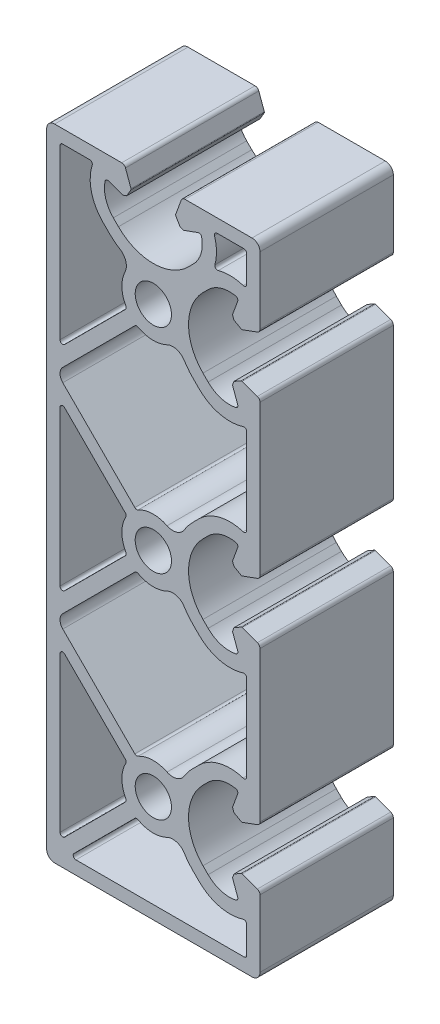
SolidWorks part; units mm, degrees
material "6005-T5"
ref_plane "Front" through (0, 0, 0) normal (0, 0, 1) x (1, 0, 0)
ref_plane "Top" through (0, 0, 0) normal (0, 1, 0) x (1, 0, 0)
ref_plane "Right" through (0, 0, 0) normal (1, 0, 0) x (0, 0, -1)
sketch "Sk Main Extrusion" plane through (0, 0, 0) normal (0, 0, 1) x (1, 0, 0)
  line L0 (-17.5, 57) -> (-17.5, 25.4749)
  line L5 (-16.6464, 25.1213) -> (-5.2369, 36.5309)
  line L6 (-8.3085, 47.4415) -> (-9.4443, 48.5773)
  line L7 (-11.9407, 57.5) -> (-17, 57.5)
  line L8 (-3.4691, 34.7631) -> (-16.9822, 21.25)
  line L9 (-16.9822, 18.75) -> (-3.4691, 5.2369)
  line L10 (7.4415, 8.3085) -> (8.5773, 9.4443)
  line L11 (17.5, 11.9407) -> (17.5, 28.0593)
  line L12 (8.5773, 30.5557) -> (7.4415, 31.6915)
  line L13 (-17.5, 14.5251) -> (-17.5, -14.5251)
  line L14 (-16.6464, -14.8787) -> (-5.2369, -3.4691)
  line L15 (-5.2369, 3.4691) -> (-16.6464, 14.8787)
  line L16 (-16.9822, -21.25) -> (-3.4691, -34.7631)
  line L17 (7.4415, -31.6915) -> (8.5773, -30.5557)
  line L18 (17.5, -28.0593) -> (17.5, -11.9407)
  line L19 (8.5773, -9.4443) -> (7.4415, -8.3085)
  line L20 (-3.4691, -5.2369) -> (-16.9822, -18.75)
  line L21 (-3.4691, -45.2369) -> (-14.8787, -56.6464)
  line L22 (-14.5251, -57.5) -> (17, -57.5)
  line L23 (17.5, -57) -> (17.5, -51.9407)
  line L24 (8.5773, -49.4443) -> (7.4415, -48.3085)
  line L25 (-17.5, -25.4749) -> (-17.5, -54.5251)
  line L26 (-16.6464, -54.8787) -> (-5.2369, -43.4691)
  line L27 (-5.2369, -36.5309) -> (-16.6464, -25.1213)
  line L28 (16.6712, 4.1901) -> (19.5065, 5.2221)
  line L29 (20, 5.9268) -> (20, 34.0732)
  line L30 (19.5065, 34.7779) -> (16.6712, 35.8099)
  line L31 (16.4607, 35.7915) -> (15.1113, 35.0124)
  line L32 (15.1113, 35.0124) -> (14.8453, 34.2815)
  line L33 (14.8453, 34.2815) -> (15.8198, 31.6038)
  line L34 (10.2727, 32.4958) -> (9.3093, 33.4593)
  line L35 (9.3093, 46.5407) -> (10.2727, 47.5042)
  line L36 (15.8198, 48.3962) -> (14.8453, 45.7185)
  line L37 (14.8453, 45.7185) -> (15.1113, 44.9876)
  line L38 (15.1113, 44.9876) -> (16.4607, 44.2085)
  line L39 (16.6712, 44.1901) -> (19.5065, 45.2221)
  line L40 (20, 45.9268) -> (20, 58.5)
  line L41 (18.5, 60) -> (5.9268, 60)
  line L42 (5.2221, 59.5065) -> (4.1901, 56.6712)
  line L43 (4.2085, 56.4607) -> (4.9876, 55.1113)
  line L44 (4.9876, 55.1113) -> (5.7185, 54.8453)
  line L45 (5.7185, 54.8453) -> (8.3962, 55.8198)
  line L46 (7.5042, 50.2727) -> (6.5407, 49.3093)
  line L47 (-6.5407, 49.3093) -> (-7.5042, 50.2727)
  line L48 (-8.3962, 55.8198) -> (-5.7185, 54.8453)
  line L49 (-5.7185, 54.8453) -> (-4.9876, 55.1113)
  line L50 (-4.9876, 55.1113) -> (-4.2085, 56.4607)
  line L51 (-4.1901, 56.6712) -> (-5.2221, 59.5065)
  line L52 (-5.9268, 60) -> (-18.5, 60)
  line L53 (-20, 58.5) -> (-20, -58.5)
  line L54 (-18.5, -60) -> (18.5, -60)
  line L55 (20, -58.5) -> (20, -45.9268)
  line L56 (19.5065, -45.2221) -> (16.6712, -44.1901)
  line L57 (16.4607, -44.2085) -> (15.1113, -44.9876)
  line L58 (15.1113, -44.9876) -> (14.8453, -45.7185)
  line L59 (14.8453, -45.7185) -> (15.8198, -48.3962)
  line L60 (10.2727, -47.5042) -> (9.3093, -46.5407)
  line L61 (9.3093, -33.4593) -> (10.2727, -32.4958)
  line L62 (15.8198, -31.6038) -> (14.8453, -34.2815)
  line L63 (14.8453, -34.2815) -> (15.1113, -35.0124)
  line L64 (15.1113, -35.0124) -> (16.4607, -35.7915)
  line L65 (16.6712, -35.8099) -> (19.5065, -34.7779)
  line L66 (20, -34.0732) -> (20, -5.9268)
  line L67 (19.5065, -5.2221) -> (16.6712, -4.1901)
  line L68 (16.4607, -4.2085) -> (15.1113, -4.9876)
  line L69 (15.1113, -4.9876) -> (14.8453, -5.7185)
  line L70 (14.8453, -5.7185) -> (15.8198, -8.3962)
  line L71 (10.2727, -7.5042) -> (9.3093, -6.5407)
  line L72 (9.3093, 6.5407) -> (10.2727, 7.5042)
  line L73 (15.8198, 8.3962) -> (14.8453, 5.7185)
  line L74 (14.8453, 5.7185) -> (15.1113, 4.9876)
  line L75 (15.1113, 4.9876) -> (16.4607, 4.2085)
  line L76 (17.5, 51.9407) -> (17.5, 57)
  line L77 (17, 57.5) -> (11.9407, 57.5)
  circle A0 centre (0, -40) radius 3.4
  circle A1 centre (0, 40) radius 3.4
  circle A2 centre (0, 0) radius 3.4
  arc A3 (-17, 57.5) -> (-17.5, 57) centre (-17, 57) ccw
  arc A4 (-17.5, 25.4749) -> (-16.6464, 25.1213) centre (-17, 25.4749) ccw
  arc A5 (-5.2369, 36.5309) -> (-5.1537, 37.1278) centre (-5.5905, 36.8844) ccw
  arc A6 (-5.3076, 42.5767) -> (-5.1537, 37.1278) centre (0, 40) ccw
  arc A7 (-5.3076, 42.5767) -> (-6.2308, 45.7881) centre (-7.5566, 43.6686) ccw
  arc A8 (-8.3085, 47.4415) -> (-6.2308, 45.7881) centre (0, 55.75) ccw
  arc A9 (-11.464, 56.8492) -> (-9.4443, 48.5773) centre (-3.646, 54.3755) ccw
  arc A10 (-11.464, 56.8492) -> (-11.9407, 57.5) centre (-11.9407, 57) ccw
  arc A11 (-2.8722, 34.8463) -> (-3.4691, 34.7631) centre (-3.1156, 34.4095) ccw
  arc A12 (-16.9822, 21.25) -> (-16.9822, 18.75) centre (-15.7322, 20) ccw
  arc A13 (-3.4691, 5.2369) -> (-2.8722, 5.1537) centre (-3.1156, 5.5905) ccw
  arc A14 (2.5767, 5.3076) -> (-2.8722, 5.1537) centre (0, 0) ccw
  arc A15 (2.5767, 5.3076) -> (5.7881, 6.2308) centre (3.6686, 7.5566) ccw
  arc A16 (19.5065, 5.2221) -> (20, 5.9268) centre (19.25, 5.9268) ccw
  arc A17 (20, 34.0732) -> (19.5065, 34.7779) centre (19.25, 34.0732) ccw
  arc A18 (16.6712, 35.8099) -> (16.4607, 35.7915) centre (16.5857, 35.575) ccw
  arc A19 (15.4507, 30.943) -> (15.8198, 31.6038) centre (15.35, 31.4328) ccw
  arc A20 (10.2727, 32.4958) -> (15.4507, 30.943) centre (14.3032, 36.5263) ccw
  arc A21 (9.3093, 46.5407) -> (9.3093, 33.4593) centre (15.85, 40) ccw
  arc A22 (15.4507, 49.057) -> (10.2727, 47.5042) centre (14.3032, 43.4737) ccw
  arc A23 (15.8198, 48.3962) -> (15.4507, 49.057) centre (15.35, 48.5672) ccw
  arc A24 (16.4607, 44.2085) -> (16.6712, 44.1901) centre (16.5857, 44.425) ccw
  arc A25 (19.5065, 45.2221) -> (20, 45.9268) centre (19.25, 45.9268) ccw
  arc A26 (20, 58.5) -> (18.5, 60) centre (18.5, 58.5) ccw
  arc A27 (5.9268, 60) -> (5.2221, 59.5065) centre (5.9268, 59.25) ccw
  arc A28 (4.1901, 56.6712) -> (4.2085, 56.4607) centre (4.425, 56.5857) ccw
  arc A29 (9.057, 55.4507) -> (8.3962, 55.8198) centre (8.5672, 55.35) ccw
  arc A30 (7.5042, 50.2727) -> (9.057, 55.4507) centre (3.4737, 54.3032) ccw
  arc A31 (-6.5407, 49.3093) -> (6.5407, 49.3093) centre (0, 55.85) ccw
  arc A32 (-9.057, 55.4507) -> (-7.5042, 50.2727) centre (-3.4737, 54.3032) ccw
  arc A33 (-8.3962, 55.8198) -> (-9.057, 55.4507) centre (-8.5672, 55.35) ccw
  arc A34 (-4.2085, 56.4607) -> (-4.1901, 56.6712) centre (-4.425, 56.5857) ccw
  arc A35 (-5.2221, 59.5065) -> (-5.9268, 60) centre (-5.9268, 59.25) ccw
  arc A36 (-18.5, 60) -> (-20, 58.5) centre (-18.5, 58.5) ccw
  arc A37 (-20, -58.5) -> (-18.5, -60) centre (-18.5, -58.5) ccw
  arc A38 (18.5, -60) -> (20, -58.5) centre (18.5, -58.5) ccw
  arc A39 (20, -45.9268) -> (19.5065, -45.2221) centre (19.25, -45.9268) ccw
  arc A40 (16.6712, -44.1901) -> (16.4607, -44.2085) centre (16.5857, -44.425) ccw
  arc A41 (15.4507, -49.057) -> (15.8198, -48.3962) centre (15.35, -48.5672) ccw
  arc A42 (10.2727, -47.5042) -> (15.4507, -49.057) centre (14.3032, -43.4737) ccw
  arc A43 (9.3093, -33.4593) -> (9.3093, -46.5407) centre (15.85, -40) ccw
  arc A44 (15.4507, -30.943) -> (10.2727, -32.4958) centre (14.3032, -36.5263) ccw
  arc A45 (15.8198, -31.6038) -> (15.4507, -30.943) centre (15.35, -31.4328) ccw
  arc A46 (16.4607, -35.7915) -> (16.6712, -35.8099) centre (16.5857, -35.575) ccw
  arc A47 (19.5065, -34.7779) -> (20, -34.0732) centre (19.25, -34.0732) ccw
  arc A48 (20, -5.9268) -> (19.5065, -5.2221) centre (19.25, -5.9268) ccw
  arc A49 (16.6712, -4.1901) -> (16.4607, -4.2085) centre (16.5857, -4.425) ccw
  arc A50 (15.4507, -9.057) -> (15.8198, -8.3962) centre (15.35, -8.5672) ccw
  arc A51 (10.2727, -7.5042) -> (15.4507, -9.057) centre (14.3032, -3.4737) ccw
  arc A52 (9.3093, 6.5407) -> (9.3093, -6.5407) centre (15.85, 0) ccw
  arc A53 (15.4507, 9.057) -> (10.2727, 7.5042) centre (14.3032, 3.4737) ccw
  arc A54 (15.8198, 8.3962) -> (15.4507, 9.057) centre (15.35, 8.5672) ccw
  arc A55 (16.4607, 4.2085) -> (16.6712, 4.1901) centre (16.5857, 4.425) ccw
  arc A56 (7.4415, 8.3085) -> (5.7881, 6.2308) centre (15.75, 0) ccw
  arc A57 (16.8492, 11.464) -> (8.5773, 9.4443) centre (14.3755, 3.646) ccw
  arc A58 (16.8492, 11.464) -> (17.5, 11.9407) centre (17, 11.9407) ccw
  arc A59 (17.5, 28.0593) -> (16.8492, 28.536) centre (17, 28.0593) ccw
  arc A60 (8.5773, 30.5557) -> (16.8492, 28.536) centre (14.3755, 36.354) ccw
  arc A61 (5.7881, 33.7692) -> (7.4415, 31.6915) centre (15.75, 40) ccw
  arc A62 (5.7881, 33.7692) -> (2.5767, 34.6924) centre (3.6686, 32.4434) ccw
  arc A63 (-2.8722, 34.8463) -> (2.5767, 34.6924) centre (0, 40) ccw
  arc A64 (-16.6464, 14.8787) -> (-17.5, 14.5251) centre (-17, 14.5251) ccw
  arc A65 (-17.5, -14.5251) -> (-16.6464, -14.8787) centre (-17, -14.5251) ccw
  arc A66 (-5.2369, -3.4691) -> (-5.1537, -2.8722) centre (-5.5905, -3.1156) ccw
  arc A67 (-5.1537, 2.8722) -> (-5.1537, -2.8722) centre (0, 0) ccw
  arc A68 (-5.1537, 2.8722) -> (-5.2369, 3.4691) centre (-5.5905, 3.1156) ccw
  arc A69 (-16.9822, -18.75) -> (-16.9822, -21.25) centre (-15.7322, -20) ccw
  arc A70 (-3.4691, -34.7631) -> (-2.8722, -34.8463) centre (-3.1156, -34.4095) ccw
  arc A71 (2.5767, -34.6924) -> (-2.8722, -34.8463) centre (0, -40) ccw
  arc A72 (2.5767, -34.6924) -> (5.7881, -33.7692) centre (3.6686, -32.4434) ccw
  arc A73 (7.4415, -31.6915) -> (5.7881, -33.7692) centre (15.75, -40) ccw
  arc A74 (16.8492, -28.536) -> (8.5773, -30.5557) centre (14.3755, -36.354) ccw
  arc A75 (16.8492, -28.536) -> (17.5, -28.0593) centre (17, -28.0593) ccw
  arc A76 (17.5, -11.9407) -> (16.8492, -11.464) centre (17, -11.9407) ccw
  arc A77 (8.5773, -9.4443) -> (16.8492, -11.464) centre (14.3755, -3.646) ccw
  arc A78 (5.7881, -6.2308) -> (7.4415, -8.3085) centre (15.75, 0) ccw
  arc A79 (5.7881, -6.2308) -> (2.5767, -5.3076) centre (3.6686, -7.5566) ccw
  arc A80 (-2.8722, -5.1537) -> (2.5767, -5.3076) centre (0, 0) ccw
  arc A81 (-2.8722, -5.1537) -> (-3.4691, -5.2369) centre (-3.1156, -5.5905) ccw
  arc A82 (-2.8722, -45.1537) -> (-3.4691, -45.2369) centre (-3.1156, -45.5905) ccw
  arc A83 (-14.8787, -56.6464) -> (-14.5251, -57.5) centre (-14.5251, -57) ccw
  arc A84 (17, -57.5) -> (17.5, -57) centre (17, -57) ccw
  arc A85 (17.5, -51.9407) -> (16.8492, -51.464) centre (17, -51.9407) ccw
  arc A86 (8.5773, -49.4443) -> (16.8492, -51.464) centre (14.3755, -43.646) ccw
  arc A87 (5.7881, -46.2308) -> (7.4415, -48.3085) centre (15.75, -40) ccw
  arc A88 (5.7881, -46.2308) -> (2.5767, -45.3076) centre (3.6686, -47.5566) ccw
  arc A89 (-2.8722, -45.1537) -> (2.5767, -45.3076) centre (0, -40) ccw
  arc A90 (-16.6464, -25.1213) -> (-17.5, -25.4749) centre (-17, -25.4749) ccw
  arc A91 (-17.5, -54.5251) -> (-16.6464, -54.8787) centre (-17, -54.5251) ccw
  arc A92 (-5.2369, -43.4691) -> (-5.1537, -42.8722) centre (-5.5905, -43.1156) ccw
  arc A93 (-5.1537, -37.1278) -> (-5.1537, -42.8722) centre (0, -40) ccw
  arc A94 (-5.1537, -37.1278) -> (-5.2369, -36.5309) centre (-5.5905, -36.8844) ccw
  arc A95 (11.9407, 57.5) -> (11.464, 56.8492) centre (11.9407, 57) ccw
  arc A96 (11.5401, 52.1568) -> (11.464, 56.8492) centre (3.646, 54.3755) ccw
  arc A97 (11.5401, 52.1568) -> (12.1568, 51.5401) centre (12.0215, 52.0215) ccw
  arc A98 (16.8492, 51.464) -> (12.1568, 51.5401) centre (14.3755, 43.646) ccw
  arc A99 (16.8492, 51.464) -> (17.5, 51.9407) centre (17, 51.9407) ccw
  arc A100 (17.5, 57) -> (17, 57.5) centre (17, 57) ccw
extrude "Main Extrusion" add sketch "Sk Main Extrusion" against normal blind 25
sketch "Threaded Insert Mate Sketch" plane through (0, 0, 0) normal (0, 0, 1) x (1, 0, 0)
  line L0 (-17.5, 0) -> (0, 0) construction
  line L1 (-17.5, 14.5251) -> (-17.5, -14.5251) construction
  circle A0 centre (0, 52.7) radius 5.6515
  circle A1 centre (0, 40) radius 3.4 construction
  circle A2 centre (12.7, 40) radius 5.6515
  circle A3 centre (0, 27.3) radius 5.6515
  circle A4 centre (-12.7, 40) radius 5.6515
  circle A5 centre (12.7, 0) radius 5.6515
  circle A6 centre (12.7, -40) radius 5.6515
  point P14 (0, 40)
  point P16 (0, 0)
equation "\"Weight kg\"= round ( \"SW-Mass\" , 2 )"
equation "\"Weight lbs\"= round ( \"SW-Mass\" * 2.2046 , 2 )"
equation "\"Length mm\"= round ( \"Length@Main Extrusion\" , 2 )"
equation "\"Length in\"= round ( \"Length@Main Extrusion\" / 25.4 , 3 )"
equation "\"D4@Threaded Insert Mate Sketch\"=\"D2@Threaded Insert Mate Sketch\""
